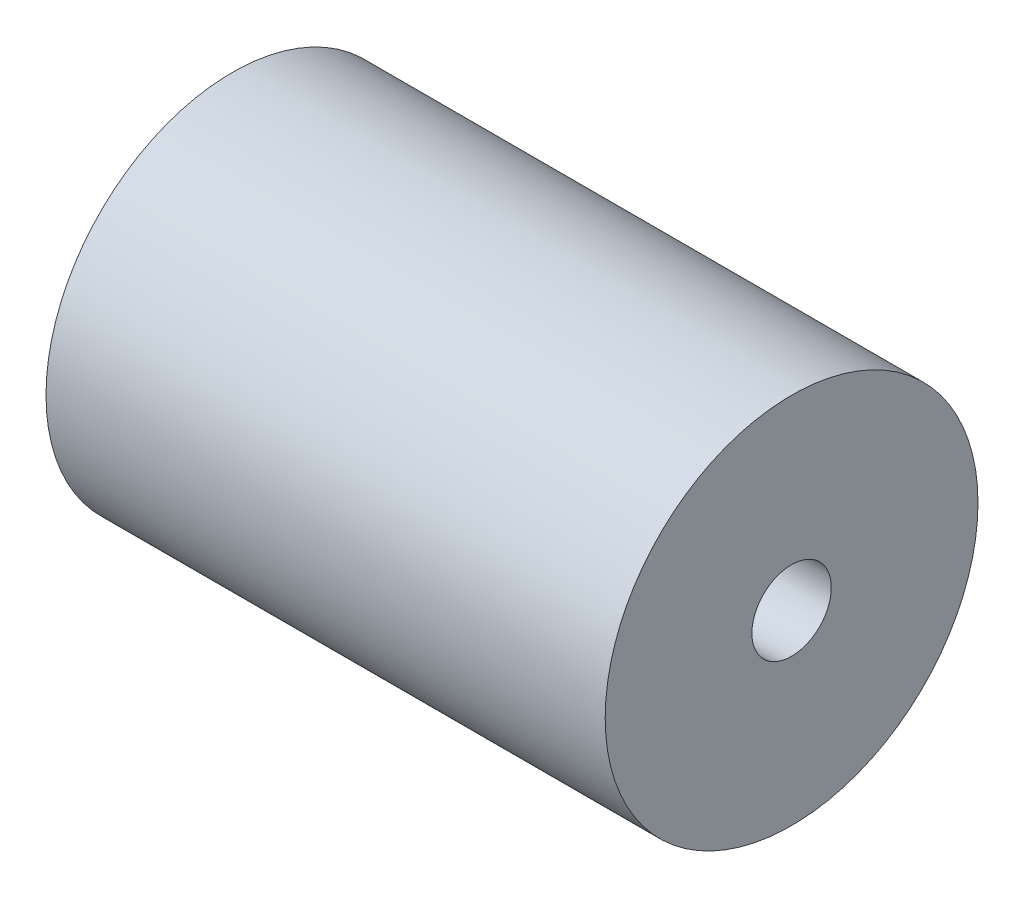
SolidWorks part; units mm, degrees
ref_plane "Front Plane" through (0, 0, 0) normal (0, 0, 1) x (1, 0, 0)
ref_plane "Top Plane" through (0, 0, 0) normal (0, 1, 0) x (1, 0, 0)
ref_plane "Right Plane" through (0, 0, 0) normal (1, 0, 0) x (0, 0, -1)
sketch "Sketch1" plane through (0, 0, 0) normal (1, 0, 0) x (0, 0, -1)
  circle A0 centre (0, 0) radius 6.35
  dimension "D1" = 12.7
extrude "Boss-Extrude1" add sketch "Sketch1" along normal blind 19.05
sketch "Sketch2" plane through (0, 0, 0) normal (-1, 0, 0) x (0, 0, 1)
  circle A0 centre (0, 0) radius 3.175
  dimension "D1" = 6.35
sketch "Sketch3" plane through (19.05, 0, 0) normal (1, 0, 0) x (0, 0, -1)
  circle A0 centre (0, 0) radius 1.5875
  dimension "D1" = 3.175
hole_wizard "#6-32 Tapped Hole1" positions "Sketch4" profile "Sketch5" tap size "#6-32" standard "ANSI Inch" end condition through all
sketch "Sketch4" plane through (0, 0, 0) normal (-1, 0, 0) x (0, 0, 1)
  point P0 (0, 0)
cosmetic thread "Hole Thread1" parameters "D2"=3.5052
sketch "Sketch5" plane through (0, 0, 0) normal (0, 1, 0) x (0, 0, 1)
  line L0 (0, 0) -> (0, 19.05)
  line L1 (0, 19.05) -> (1.3525, 19.05)
  line L2 (1.3525, 19.05) -> (1.3525, 0)
  line L5 (1.3525, 0) -> (0, 0)
  line L11 (0, -6.35) -> (0, 107.95) construction
  dimension "Thru Tap Drill Dia." = 2.7051
  dimension "Thru Tap Drill Depth" = 19.05
